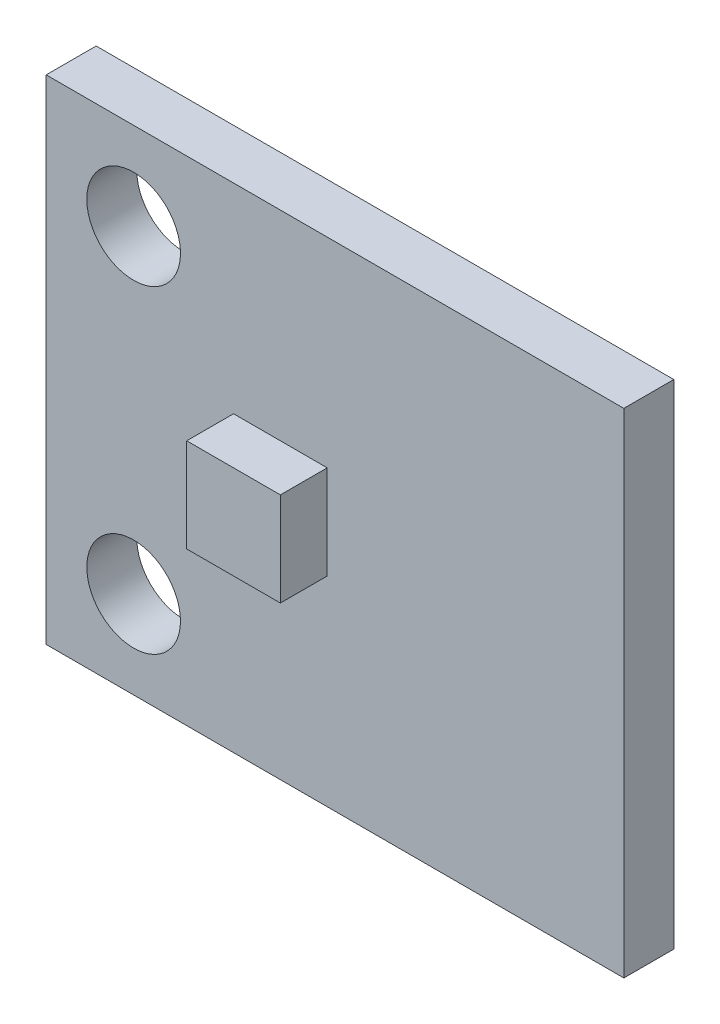
SolidWorks part; units mm, degrees
ref_plane "Płaszczyzna przednia" through (0, 0, 0) normal (0, 0, 1) x (1, 0, 0)
ref_plane "Płaszczyzna górna" through (0, 0, 0) normal (0, 1, 0) x (1, 0, 0)
ref_plane "Płaszczyzna prawa" through (0, 0, 0) normal (1, 0, 0) x (0, 0, -1)
sketch "Szkic1" plane through (0, 0, 0) normal (0, 0, 1) x (1, 0, 0)
  line L5 (0, 0) -> (18.5, 0)
  line L6 (0, 0) -> (0, 15.8)
  line L7 (0, 15.8) -> (18.5, 15.8)
  line L8 (18.5, 0) -> (18.5, 15.8)
  dimension "D3" = 18.5
  dimension "D4" = 15.8
extrude "Dodanie-wyciągnięcie1" add sketch "Szkic1" along normal blind 1.6
sketch "Szkic2" plane through (0, 0, 0) normal (0, 0, -1) x (-1, 0, 0)
  line L0 (-18.5, 15.8) -> (0, 15.8) construction
  line L1 (-2.8, 14.5) -> (-2.8, 13) construction
  line L2 (-2.8, 13) -> (-1.3, 13) construction
  line L3 (0, 15.8) -> (0, 0) construction
  line L4 (-18.5, 7.9) -> (0, 7.9) construction
  line L5 (-18.5, 0) -> (-18.5, 15.8) construction
  circle A0 centre (-2.8, 13) radius 1.5
  circle A1 centre (-2.8, 2.8) radius 1.5
  dimension "D1" = 3
  dimension "D2" = 1.3
  dimension "D3" = 1.3
extrude "Wytnij-wyciągnięcie1" cut sketch "Szkic2" against normal through all
sketch "Szkic3" plane through (0, 0, 1.6) normal (0, 0, 1) x (1, 0, 0)
  line L0 (0, 7.9) -> (18.5, 7.9) construction
  line L1 (6, 9.4) -> (9, 9.4)
  line L2 (6, 9.4) -> (6, 6.4)
  line L3 (6, 6.4) -> (9, 6.4)
  line L4 (9, 9.4) -> (9, 6.4)
  line L5 (0, 15.8) -> (0, 0) construction
  line L6 (18.5, 0) -> (18.5, 15.8) construction
  line L7 (6, 7.9) -> (9, 7.9) construction
  dimension "D1" = 3
  dimension "D2" = 3
  dimension "D3" = 6
extrude "Dodanie-wyciągnięcie2" add sketch "Szkic3" along normal blind 1.5
